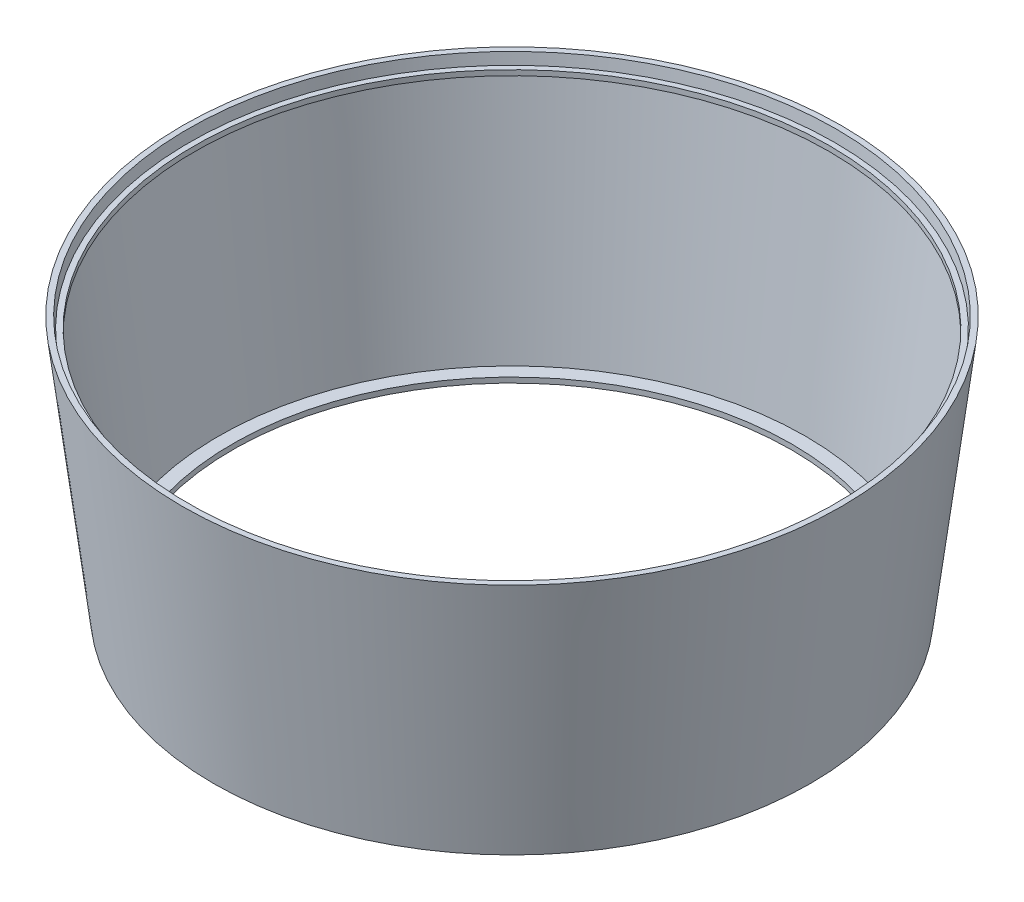
SolidWorks part; units mm, degrees
ref_plane "前视基准面" through (0, 0, 0) normal (0, 0, 1) x (1, 0, 0)
ref_plane "上视基准面" through (0, 0, 0) normal (0, 1, 0) x (1, 0, 0)
ref_plane "右视基准面" through (0, 0, 0) normal (1, 0, 0) x (0, 0, -1)
sketch "草图1" plane through (0, 0, 0) normal (0, 0, 1) x (1, 0, 0)
  line L0 (0, 0) -> (50, 0)
  line L1 (0, 0) -> (0, 14)
  line L2 (50, 0) -> (134.4555, 687.8345)
  line L3 (134.4555, 687.8345) -> (119.4555, 687.8345)
  line L4 (119.4555, 687.8345) -> (115.7994, 658.0581)
  line L5 (115.7994, 658.0581) -> (101.3594, 658.0581)
  line L6 (101.3594, 658.0581) -> (101.3594, 644.0581)
  line L7 (114.0804, 644.0581) -> (36.719, 14)
  line L8 (101.3594, 644.0581) -> (114.0804, 644.0581)
  line L9 (0, 14) -> (36.719, 14)
  line L10 (0, 0) -> (-752, 0) construction
  line L11 (-752, 0) -> (-752, 109.4948) construction
revolve "旋转1" add sketch "草图1" angle 360 about L11
